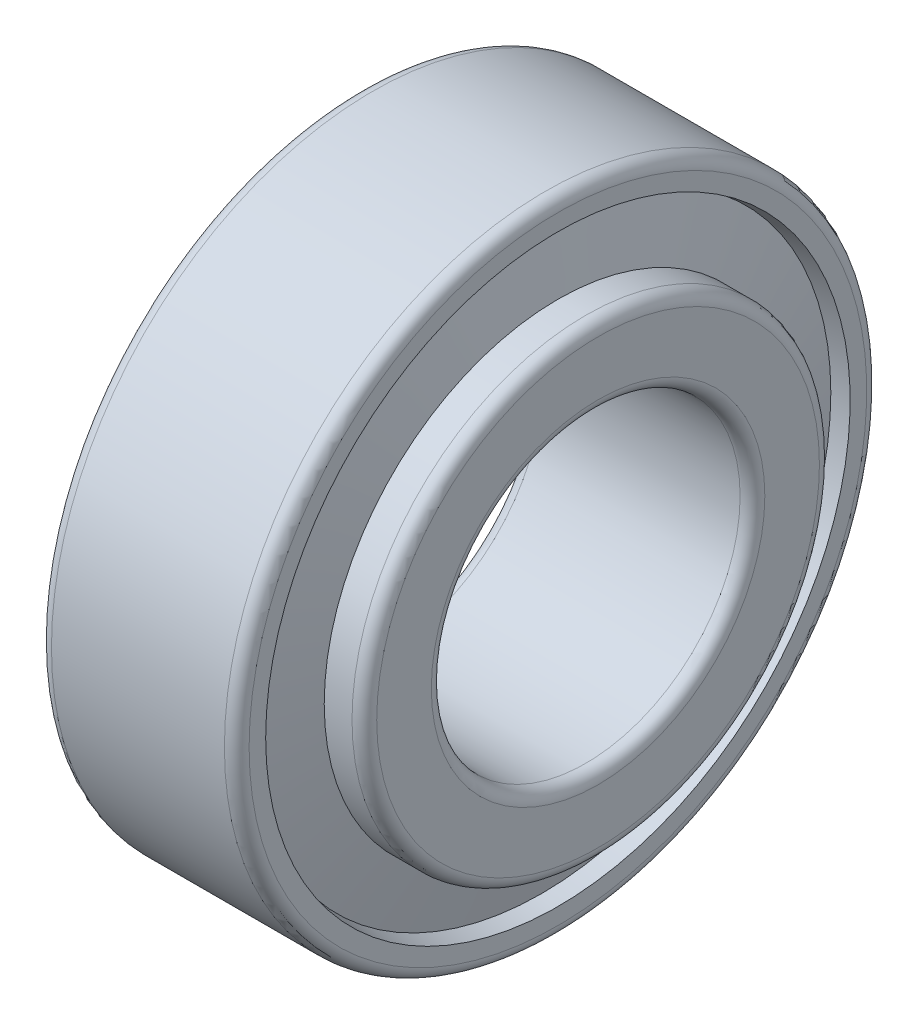
SolidWorks part; units mm, degrees
material "AISI Тип A2 Инструментальная сталь"
ref_plane "Спереди" through (0, 0, 0) normal (0, 0, 1) x (1, 0, 0)
ref_plane "Сверху" through (0, 0, 0) normal (0, 1, 0) x (1, 0, 0)
ref_plane "Справа" through (0, 0, 0) normal (1, 0, 0) x (0, 0, -1)
sketch "Эскиз1" plane through (0, 0, 0) normal (0, 0, 1) x (1, 0, 0)
  line L20 (-882.5277, 0) -> (43243.8573, 0) construction
  line L33 (2.8534, 21.1993) -> (0, 20.6655)
  line L34 (0, 20.6655) -> (0, 25)
  line L35 (1, 26) -> (15, 26)
  line L36 (16, 25) -> (16, 23.6585)
  line L37 (16, 23.6585) -> (14.6813, 23.4118)
  line L38 (2.8534, 21.1993) -> (14.6813, 23.4118) construction
  line L39 (4.4567, 14.5208) -> (1.25, 14.5208)
  line L40 (1.25, 14.5208) -> (1.25, 13.5)
  line L41 (2.25, 12.5) -> (18.25, 12.5)
  line L42 (19.25, 13.5) -> (19.25, 17.9192)
  line L43 (18.25, 18.9192) -> (16, 18.9192)
  line L44 (16, 18.9192) -> (16, 17.9192)
  line L45 (4.4567, 14.5208) -> (16, 17.9192) construction
  line L46 (16, 17.9192) -> (14.6813, 23.4118)
  line L47 (4.4567, 14.5208) -> (2.8534, 21.1993)
  line L48 (3.655, 17.86) -> (15.3407, 20.6655) construction
  line L49 (0, 20.6655) -> (15.3407, 20.6655) construction
  line L50 (2.8534, 21.1993) -> (2.8534, 14.5208) construction
  arc A0 (0, 25) -> (1, 26) centre (1, 25) cw
  arc A1 (15, 26) -> (16, 25) centre (15, 25) cw
  arc A2 (1.25, 13.5) -> (2.25, 12.5) centre (2.25, 13.5) ccw
  arc A3 (19.25, 13.5) -> (18.25, 12.5) centre (18.25, 13.5) cw
  arc A4 (18.25, 18.9192) -> (19.25, 17.9192) centre (18.25, 17.9192) cw
  point P12 (15.3407, 20.6655)
  dimension "гост r1" = 1
  dimension "гост r2" = 1
  dimension "гост DD" = 52
  dimension "гост B" = 18
  dimension "гост C" = 16
  dimension "гост T" = 19.25
  dimension "гост E" = 41.331
  dimension "гост d" = 25
  dimension "гост alfa" = 13.5
revolve "Повернуть1" add sketch "Эскиз1" angle 360 about L20
